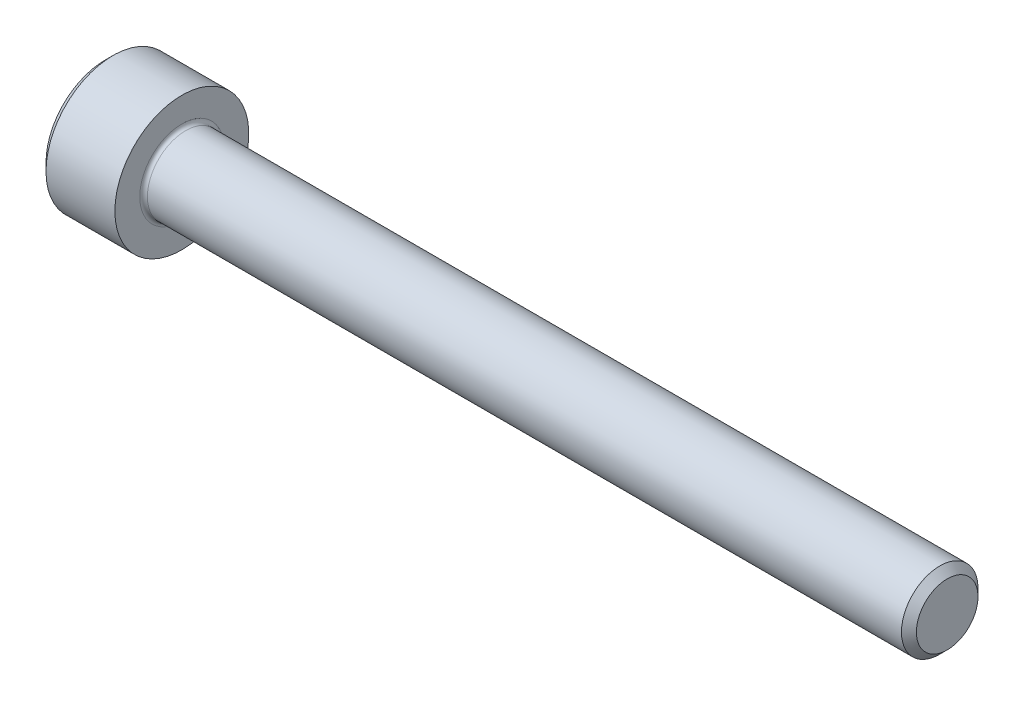
SolidWorks part; units mm, degrees
revolve "Base-Revolve" add sketch "BodySke"
sketch "BodySke" plane through (0, 0, 0) normal (0, 0, 1) x (1, 0, 0)
  line L0 (0, 0) -> (0, 3.1)
  line L1 (0.4, 3.5) -> (4, 3.5)
  line L2 (4, 3.5) -> (4, 2)
  line L3 (4, 2) -> (43.61, 2)
  line L4 (44, 1.61) -> (44, 0)
  line L5 (44, 0) -> (0, 0)
  line L6 (-31.75, 0) -> (127, 0) construction
  line L7 (0, 3.1) -> (0.4, 3.5)
  line L8 (44, 1.61) -> (43.61, 2)
  line L9 (0, -3.1) -> (0.4, -3.5) construction
  line L10 (44, -1.61) -> (43.61, -2) construction
  line L11 (4.7, 9.525) -> (4.7, 3.175) construction
  line L12 (24, 9.525) -> (24, 3.175) construction
  line L13 (-6, 9.525) -> (-6, 3.175) construction
  dimension "Diameter" = 4
  dimension "Head_ht" = 4
  dimension "Length" = 40
  dimension "Body_ch_ang" = 45
  dimension "Head_dia" = 7
  dimension "Head_ch_ang" = 45
  dimension "Minor_dia" = 3.22
  dimension "Advance" = 0.7
  dimension "Thread_nom" = 20
  dimension "Thread_length" = 50
  dimension "Head_ch_ht" = 0.4
cosmetic thread "ThreadCosmetic"
fillet "Fillet1" radius 0.2 1 edges at (4, 0, 2)
ref_plane "Plane1" through (0, 0, 0) normal (0, 0, 1) x (1, 0, 0)
ref_plane "Plane2" through (0, 0, 0) normal (0, 1, 0) x (1, 0, 0)
ref_plane "Plane3" through (0, 0, 0) normal (1, 0, 0) x (0, 0, -1)
other "Configuration Table"
sketch "Sketch2" plane through (0, 0, 0) normal (0, 0, 1) x (1, 0, 0)
  line L0 (0, 1.5355) -> (2, 1.5355)
  line L1 (2, 1.5355) -> (2.8865, 0)
  line L2 (-31.75, 0) -> (127, 0) construction
  line L3 (2.8865, 0) -> (0, 0)
  line L4 (0, 0) -> (0, 1.5355)
  line L5 (0, 3.1) -> (0, -3.1) construction
  line L6 (0, 0) -> (47.625, 0) construction
  line L7 (4, -3.5) -> (4, 3.5) construction
  dimension "D1" = 1.5355
  dimension "D2" = 60
revolve "Hex-PreBroach" cut sketch "Sketch2" angle 360 about L6
sketch "Sketch3" plane through (0, 0, 0) normal (-1, 0, 0) x (0, 0.5, 0.866)
  line L0 (0.8865, 1.5355) -> (-0.8865, 1.5355)
  line L1 (-0.8865, 1.5355) -> (-1.773, 0)
  line L2 (0.8865, 1.5355) -> (1.773, 0)
  line L3 (0.8865, -1.5355) -> (1.773, 0)
  line L4 (0.8865, -1.5355) -> (-0.8865, -1.5355)
  line L5 (-0.8865, -1.5355) -> (-1.773, 0)
  dimension "D1" = 1.5355
  dimension "D2" = 1.5355
  dimension "Hex_size" = 3.071
extrude "Hex" cut sketch "Sketch3" against normal blind 2
sketch "Sketch4" plane through (0, 0, 0) normal (-1, 0, 0) x (0, 0, 1)
  line L0 (0, 0) -> (1.7399, 0)
  line L1 (0, 0) -> (6.1484, 3.5498) construction
  line L2 (0, 0) -> (0.8699, 1.5068)
  line L3 (1.4457, 0.3947) -> (1.6607, 0.5189)
  line L4 (1.0647, 1.0546) -> (1.2797, 1.1788)
  arc A0 (1.4457, 0.3947) -> (1.0647, 1.0546) centre (0, 0) ccw
  arc A1 (1.7399, 0) -> (1.6607, 0.5189) centre (0, 0) ccw
  arc A2 (0.8699, 1.5068) -> (1.2797, 1.1788) centre (0, 0) cw
  dimension "D1" = 30
  dimension "D2" = 60
  dimension "Spline_p_dim" = 0.762
  dimension "D3" = 0.381
extrude "Spline" [suppressed] cut sketch "Sketch4" against normal blind 2
pattern_circular "CirPattern1" [suppressed] count 6 every 60
sketch "Sketch5" plane through (0, 0, 0) normal (0, 0, 1) x (1, 0, 0)
  line L0 (-31.75, 0) -> (127, 0) construction
  line L2 (0, 3.1) -> (0, -3.1) construction
  circle A0 centre (1.6, 0) radius 0.675
  dimension "Drilled_hole_dia" = 1.35
  dimension "Drilled_hole_loc" = 1.6
extrude "Hole" [suppressed] cut sketch "Sketch5" against normal through all and the other way through all
pattern_circular "Drilled-4" [suppressed] count 2 every 60
pattern_circular "Drilled-6" [suppressed] count 3 every 60
sketch "ThdSchSke" plane through (0, 0, 0) normal (0, 0, 1) x (1, 0, 0)
  line L0 (24, -1.61) -> (23.7269, -2)
  line L1 (24, -1.61) -> (24.2731, -2)
  line L2 (24.2731, -2) -> (24.2731, -2.5)
  line L3 (-3.175, 0) -> (5.1513, 0) construction
  line L5 (24.2731, -2.5) -> (23.7269, -2.5)
  line L6 (23.7269, -2.5) -> (23.7269, -2)
  line L7 (0, 3.1) -> (0, -3.1) construction
  dimension "Thread_minor" = 3.22
  dimension "Diameter" = 4
revolve "ThreadSchematic" [suppressed] cut sketch "ThdSchSke" angle 360 about L3
pattern_linear "ThdSchPat" [suppressed]
equation "\"D2@Sketch3\" = \"Hex_size@Sketch3\" / 2"
equation "\"D1@Sketch3\" = \"Hex_size@Sketch3\" / 2"
equation "\"D1@Sketch2\" = \"Hex_size@Sketch3\" / 2"
equation "\"D3@Sketch4\" = \"Spline_p_dim@Sketch4\" / 2"
equation "\"Thread_minor@ThreadCosmetic\"  =  \"Minor_dia@BodySke\""
equation "\"D2@CirPattern1\" = 360 / \"Num_teeth@CirPattern1\""
equation "\"Wall_thickness@Sketch2\" = \"Head_ht@BodySke\" - \"Key_eng@Hex\""
equation "\"Thread_length@ThreadCosmetic\" = ((sgn( (\"Length@BodySke\" - \"Advance@BodySke\" ) - \"Thread_nom@BodySke\" )-1)*( (\"Length@BodySke\" - \"Advance@BodySke\" ) - \"Thread_nom@BodySke\" ))/-2+ \"Thread_nom@BodySke\""
equation "\"Thread_minor@ThdSchSke\" = \"Minor_dia@BodySke\""
equation "\"Diameter@ThdSchSke\" = \"Diameter@BodySke\""
equation "\"Overcut@ThdSchSke\" = \"Diameter@BodySke\" * 1.25"
equation "\"Start@ThdSchSke\" = \"Head_ht@BodySke\" + \"Length@BodySke\" - \"Thread_length@ThreadCosmetic\"  '---Non-countersunk---"
equation "\"Num_threads@ThdSchPat\" = int( \"Thread_length@ThreadCosmetic\" / \"Advance@BodySke\" + 0.999 )  + 1"
equation "\"Advance@ThdSchPat\" = \"Thread_length@ThreadCosmetic\" /  (\"Num_threads@ThdSchPat\" - 1) 'relax it"
equation "\"Num_threads@ThdSchPat\" = \"Num_threads@ThdSchPat\" - sgn( \"Num_threads@ThdSchPat\" - 1) '---chamfered tips only---"
